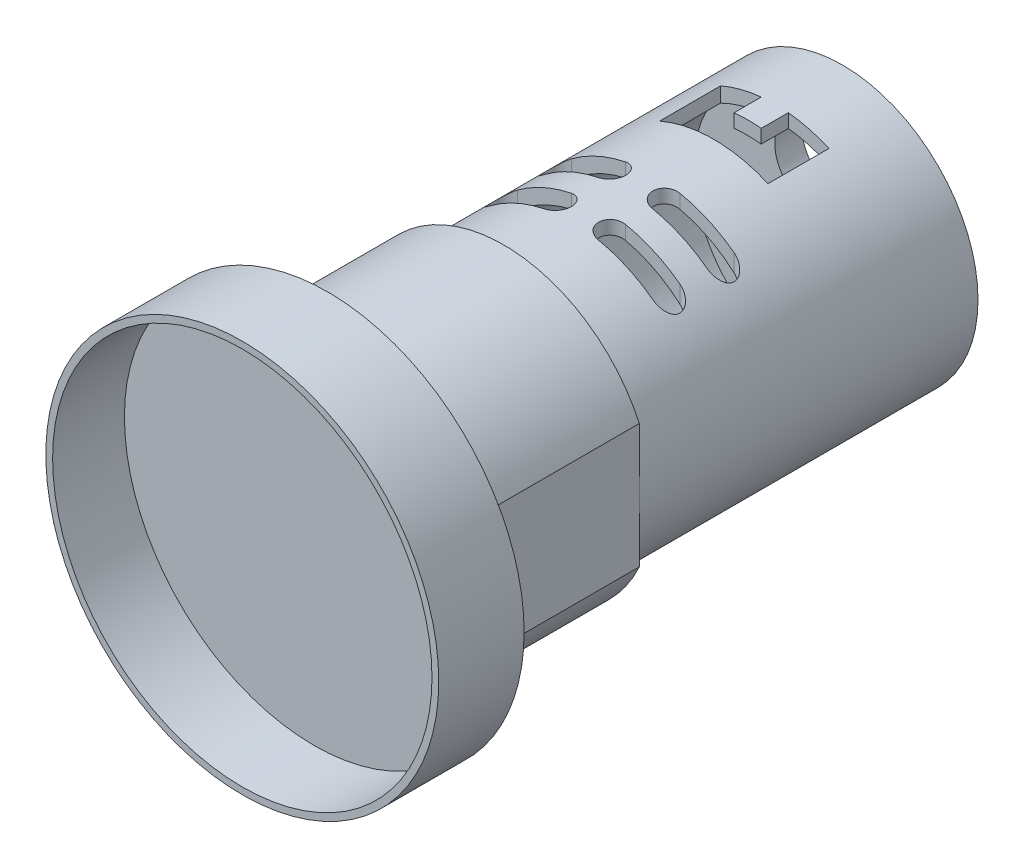
SolidWorks part; units mm, degrees
ref_plane "Front Plane" through (0, 0, 0) normal (0, 0, 1) x (1, 0, 0)
ref_plane "Top Plane" through (0, 0, 0) normal (0, 1, 0) x (1, 0, 0)
ref_plane "Right Plane" through (0, 0, 0) normal (1, 0, 0) x (0, 0, -1)
sketch "Sketch1" plane through (0, 0, 0) normal (0, 0, 1) x (1, 0, 0)
  circle A0 centre (0, 0) radius 10
  dimension "D1" = 20
extrude "Boss-Extrude1" add sketch "Sketch1" along normal blind 38
sketch "Sketch2" plane through (0, 0, 38) normal (0, 0, 1) x (1, 0, 0)
  circle A0 centre (0, 0) radius 14.5
  dimension "D1" = 29
extrude "Boss-Extrude2" add sketch "Sketch2" along normal blind 1
sketch "Sketch3" plane through (0, 0, 39) normal (0, 0, 1) x (1, 0, 0)
  circle A0 centre (0, 0) radius 14.5
  circle A1 centre (0, 0) radius 14
  dimension "D1" = 28
  dimension "D2" = 29
extrude "Boss-Extrude3" add sketch "Sketch3" along normal blind 5.3
sketch "Sketch4" plane through (0, 0, 38) normal (0, 0, -1) x (-1, 0, 0)
  circle A0 centre (0, 0) radius 11
  dimension "D1" = 22
extrude "Boss-Extrude4" add sketch "Sketch4" along normal blind 13
sketch "Sketch6" plane through (0, 0, 0) normal (0, 0, -1) x (-1, 0, 0)
  line L0 (0, 10) -> (0, -10) construction
  circle A0 centre (0, 4.5) radius 3
  circle A1 centre (0, -4.5) radius 3
  circle A2 centre (0, 0) radius 10 construction
  circle A3 centre (0, 0) radius 10 construction
  dimension "D1" = 6
  dimension "D2" = 9
  dimension "D3" = 4.5
extrude "Cut-Extrude2" cut sketch "Sketch6" against normal blind 9
sketch "Sketch7" plane through (0, 0, 0) normal (0, 1, 0) x (1, 0, 0)
  line L0 (0, 0) -> (0, -44.3) construction
  line L1 (-4, -5) -> (0, -5) construction
  line L2 (-4, -5) -> (-4, -9.5)
  line L3 (-4, -9.5) -> (4, -9.5)
  line L4 (6, -16) -> (2, -16)
  line L5 (-14.5, -44.3) -> (14.5, -44.3) construction
  line L6 (10, 0) -> (-10, 0) construction
  line L7 (-4, -5) -> (-1, -5)
  line L8 (-1, -5) -> (-1, -7)
  line L9 (-1, -7) -> (1, -7)
  line L10 (4, -5) -> (4, -9.5)
  line L11 (4, -5) -> (1, -5)
  line L12 (1, -5) -> (1, -7)
  line L13 (-6, -15) -> (6, -15) construction
  line L14 (6, -14) -> (2, -14)
  line L15 (-6, -17) -> (6, -17) construction
  line L16 (-6, -14) -> (-2, -14)
  line L17 (6, -18) -> (2, -18)
  line L18 (-6, -16) -> (-2, -16)
  line L19 (6, -20) -> (2, -20)
  line L20 (-6, -20) -> (-2, -20)
  line L21 (-6, -18) -> (-2, -18)
  arc A0 (-6, -14) -> (-6, -16) centre (-6, -15) ccw
  arc A1 (-2, -16) -> (-2, -14) centre (-2, -15) ccw
  arc A2 (6, -14) -> (6, -16) centre (6, -15) cw
  arc A3 (2, -16) -> (2, -14) centre (2, -15) cw
  arc A4 (-6, -20) -> (-6, -18) centre (-6, -19) cw
  arc A5 (-2, -18) -> (-2, -20) centre (-2, -19) cw
  arc A6 (2, -18) -> (2, -20) centre (2, -19) ccw
  arc A7 (6, -20) -> (6, -18) centre (6, -19) ccw
  point P15 (0, -9.5)
  point P18 (0, -7)
  point P22 (0, -15)
  point P33 (0, -17)
  dimension "D6" = 2
  dimension "D7" = 2
  dimension "D10" = 5.5
  dimension "D1" = 4
  dimension "D2" = 5
  dimension "D3" = 1
  dimension "D4" = 2
  dimension "D5" = 4.5
  dimension "D8" = 4
  dimension "D9" = 2
  dimension "D11" = 2
extrude "Cut-Extrude3" cut sketch "Sketch7" against normal through all and the other way through all
ref_plane "Plane2" through (0, 0, 19) normal (0, 0, 1) x (1, 0, 0)
sketch "Sketch8" plane through (0, 0, 19) normal (0, 0, 1) x (1, 0, 0)
  circle A0 centre (0, 0) radius 9
  dimension "D1" = 18
extrude "Cut-Extrude4" cut sketch "Sketch8" against normal blind 17 and the other way blind 17
sketch "Sketch5" plane through (0, 0, 0) normal (0, 0, -1) x (-1, 0, 0)
  line L1 (-10, 20) -> (10, 20)
  line L2 (-10, 20) -> (-10, -20)
  line L3 (-10, -20) -> (10, -20)
  line L4 (10, 20) -> (10, -20)
  line L5 (-15, 20) -> (15, 20)
  line L6 (-15, 20) -> (-15, -20)
  line L7 (-15, -20) -> (15, -20)
  line L8 (15, 20) -> (15, -20)
  circle A0 centre (0, 0) radius 10 construction
  circle A1 centre (0, 0) radius 10 construction
  dimension "D1" = 20
  dimension "D2" = 20
  dimension "D3" = 5
  dimension "D4" = 5
extrude "Cut-Extrude1" cut sketch "Sketch5" against normal up to surface (38 mm away) contours L6 L7 L2 L5 | L8 L5 L4 L7 up to face at (14.5, 0, 38)
